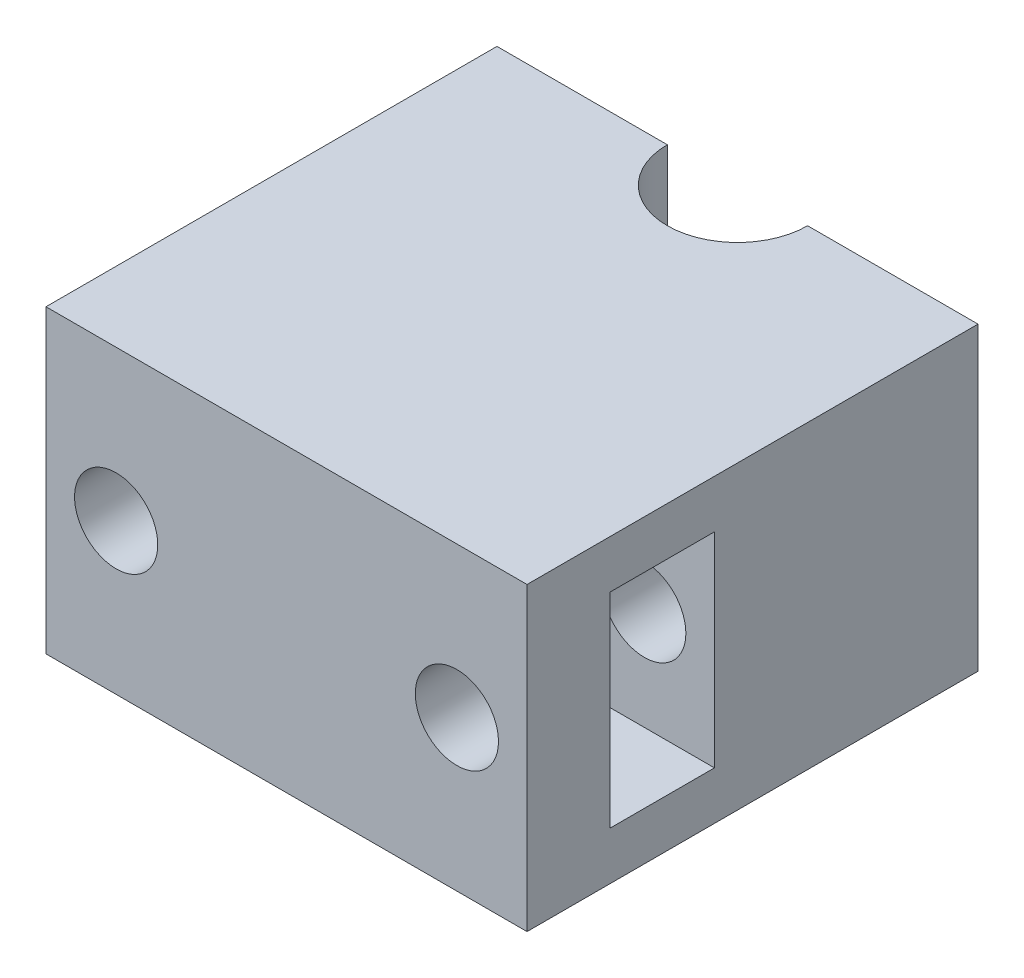
SolidWorks part; units mm, degrees
ref_plane "Спереди" through (0, 0, 0) normal (0, 0, 1) x (1, 0, 0)
ref_plane "Сверху" through (0, 0, 0) normal (0, 1, 0) x (1, 0, 0)
ref_plane "Справа" through (0, 0, 0) normal (1, 0, 0) x (0, 0, -1)
sketch "Sketch1" plane through (0, 0, 0) normal (0, 1, 0) x (1, 0, 0)
  line L1 (24, -22.5) -> (-24, -22.5)
  line L2 (24, -22.5) -> (24, 22.5)
  line L3 (24, 22.5) -> (-24, 22.5)
  line L4 (-24, -22.5) -> (-24, 22.5)
  line L5 (24, -22.5) -> (-24, 22.5) construction
  line L6 (24, 22.5) -> (-24, -22.5) construction
  point P0 (0, 0)
  dimension "D1" = 48
  dimension "D2" = 45
extrude "Boss-Extrude1" add sketch "Sketch1" along normal blind 30
sketch "Sketch2" plane through (24, 0, 0) normal (1, 0, 0) x (0, 0, -1)
  line L0 (-22.5, 15) -> (22.5, 15) construction
  line L1 (-22.5, 30) -> (-22.5, 0) construction
  line L2 (22.5, 30) -> (22.5, 0) construction
  line L4 (-14.2, 4.8) -> (-3.8, 4.8)
  line L5 (-14.2, 4.8) -> (-14.2, 25.2)
  line L6 (-14.2, 25.2) -> (-3.8, 25.2)
  line L7 (-3.8, 4.8) -> (-3.8, 25.2)
  line L8 (-14.2, 4.8) -> (-3.8, 25.2) construction
  line L9 (-14.2, 25.2) -> (-3.8, 4.8) construction
  point P6 (-9, 15)
  dimension "D1" = 10.4
  dimension "D2" = 20.4
  dimension "D3" = 31.5
extrude "Cut-Extrude1" cut sketch "Sketch2" against normal through all
sketch "Sketch3" plane through (0, 0, 22.5) normal (0, 0, 1) x (1, 0, 0)
  line L0 (-24, 15) -> (24, 15) construction
  line L1 (-24, 30) -> (-24, 0) construction
  line L2 (24, 30) -> (24, 0) construction
  circle A0 centre (-17, 15) radius 4.15
  circle A1 centre (17, 15) radius 4.15
  point P10 (0, 15)
  dimension "D1" = 34
  dimension "D2" = 8.3
  dimension "D3" = 17
extrude "Cut-Extrude2" cut sketch "Sketch3" against normal through all
sketch "Sketch4" plane through (0, 30, 0) normal (0, 1, 0) x (1, 0, 0)
  line L0 (0, 22.5) -> (0, -22.5) construction
  line L1 (24, 22.5) -> (-24, 22.5) construction
  line L2 (-24, -22.5) -> (24, -22.5) construction
  arc A0 (-7, 22.5) -> (7, 22.5) centre (0, 22.5) ccw
  dimension "D1" = 7
extrude "Cut-Extrude3" cut sketch "Sketch4" against normal through all and the other way through all
